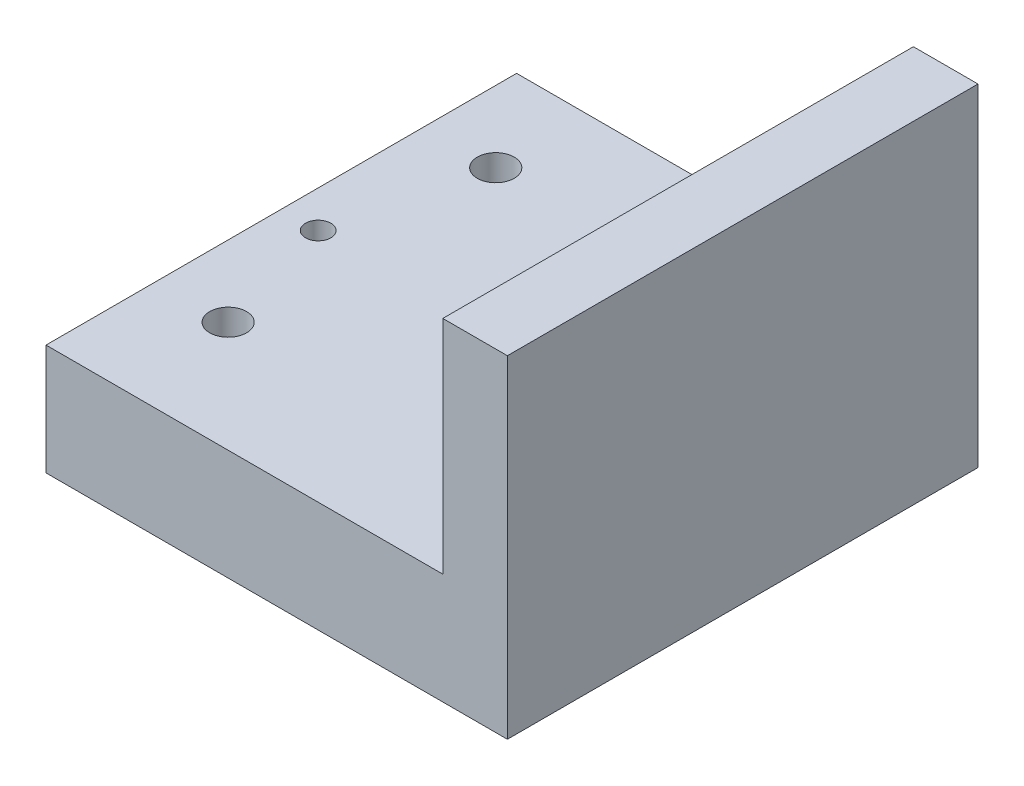
SolidWorks part; units mm, degrees
ref_plane "Front Plane" through (0, 0, 0) normal (0, 0, 1) x (1, 0, 0)
ref_plane "Top Plane" through (0, 0, 0) normal (0, 1, 0) x (1, 0, 0)
ref_plane "Right Plane" through (0, 0, 0) normal (1, 0, 0) x (0, 0, -1)
sketch "Sketch1" plane through (0, 0, 0) normal (0, 1, 0) x (1, 0, 0)
  line L1 (-21.5, 25.5) -> (21.5, 25.5)
  line L2 (-21.5, 25.5) -> (-21.5, -25.5)
  line L3 (-21.5, -25.5) -> (21.5, -25.5)
  line L4 (21.5, 25.5) -> (21.5, -25.5)
  dimension "D1" = 43
  dimension "D2" = 51
  dimension "D3" = 21.5
  dimension "D4" = 25.5
extrude "Boss-Extrude1" add sketch "Sketch1" along normal blind 12
sketch "Sketch2" plane through (0, 12, 0) normal (0, 1, 0) x (1, 0, 0)
  line L1 (21.5, 25.5) -> (28.5, 25.5)
  line L2 (21.5, 25.5) -> (21.5, -25.5)
  line L3 (21.5, -25.5) -> (28.5, -25.5)
  line L4 (28.5, 25.5) -> (28.5, -25.5)
  dimension "D1" = 7
extrude "Boss-Extrude2" add sketch "Sketch2" along normal blind 24 and the other way blind 12
sketch "Sketch3" plane through (0, 12, 0) normal (0, 1, 0) x (1, 0, 0)
  line L0 (21.5, -25.5) -> (21.5, 25.5) construction
  circle A0 centre (17.5, 0) radius 1.375
  circle A1 centre (-17.5, 0) radius 1.375
  circle A2 centre (13.775, 15.5138) radius 2
  circle A3 centre (-13.775, 15.5138) radius 2
  circle A4 centre (13.775, -13.4862) radius 2
  circle A5 centre (-13.775, -13.4862) radius 2
  dimension "D1" = 4
  dimension "D3" = 7.725
  dimension "D2" = 2
  dimension "D4" = 2
  dimension "D5" = 2
  dimension "D6" = 2
extrude "Cut-Extrude1" cut sketch "Sketch3" against normal blind 12
